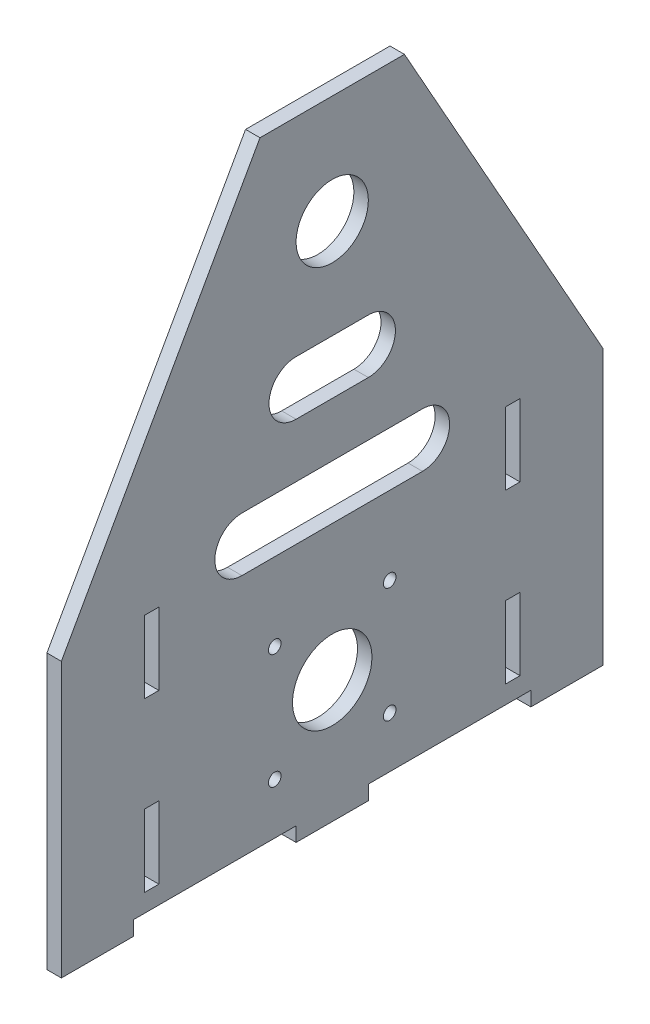
SolidWorks part; units mm, degrees
ref_plane "Front Plane" through (0, 0, 0) normal (0, 0, 1) x (1, 0, 0)
ref_plane "Top Plane" through (0, 0, 0) normal (0, 1, 0) x (1, 0, 0)
ref_plane "Right Plane" through (0, 0, 0) normal (1, 0, 0) x (0, 0, -1)
sketch "Sketch1" plane through (0, 0, 0) normal (1, 0, 0) x (0, 0, -1)
  line L0 (0, 0) -> (0, 111.6623) construction
  line L1 (-20, 170.0871) -> (20, 170.0871)
  line L2 (-55, 0.0871) -> (-10, 0.0871)
  line L3 (-75, -3.9129) -> (-75, 72.0364)
  line L4 (-75, 72.0364) -> (-20, 170.0871)
  line L5 (20, 170.0871) -> (75, 72.0364)
  line L6 (75, 72.0364) -> (75, -3.9129)
  line L7 (-75, -3.9129) -> (-55, -3.9129)
  line L8 (-55, 0.0871) -> (-55, -3.9129)
  line L9 (-10, 0.0871) -> (-10, -3.9129)
  line L10 (10, 0.0871) -> (10, -3.9129)
  line L11 (55, 0.0871) -> (55, -3.9129)
  line L12 (-10, -3.9129) -> (10, -3.9129)
  line L13 (55, -3.9129) -> (75, -3.9129)
  line L14 (10, 0.0871) -> (55, 0.0871)
  line L15 (0, 30.0871) -> (-15.9099, 45.997) construction
  line L16 (-25, 75.0871) -> (25, 75.0871) construction
  line L17 (-10, 105.0871) -> (10, 105.0871) construction
  line L18 (-10, 105.0871) -> (10, 105.0871) construction
  line L19 (-10, 112.5871) -> (10, 112.5871)
  line L20 (-10, 97.5871) -> (10, 97.5871)
  line L21 (-25, 75.0871) -> (25, 75.0871) construction
  line L22 (-25, 82.5871) -> (25, 82.5871)
  line L23 (-25, 67.5871) -> (25, 67.5871)
  line L24 (-50, 169.5343) -> (-50, -42.818) construction
  line L25 (50, 169.5343) -> (50, -42.818) construction
  line L26 (-62.1844, 15.0871) -> (92.4546, 15.0871) construction
  line L27 (-91.6692, 61.5499) -> (106.6605, 61.5499) construction
  line L28 (-52, 25.0871) -> (-48, 25.0871)
  line L29 (-52, 25.0871) -> (-52, 5.0871)
  line L30 (-52, 5.0871) -> (-48, 5.0871)
  line L31 (-48, 25.0871) -> (-48, 5.0871)
  line L32 (-52, 25.0871) -> (-48, 5.0871) construction
  line L33 (-52, 5.0871) -> (-48, 25.0871) construction
  line L34 (48, 25.0871) -> (52, 25.0871)
  line L35 (48, 25.0871) -> (48, 5.0871)
  line L36 (48, 5.0871) -> (52, 5.0871)
  line L37 (52, 25.0871) -> (52, 5.0871)
  line L38 (48, 25.0871) -> (52, 5.0871) construction
  line L39 (48, 5.0871) -> (52, 25.0871) construction
  line L41 (-52, 71.5499) -> (-48, 71.5499)
  line L42 (-52, 71.5499) -> (-52, 51.5499)
  line L43 (-52, 51.5499) -> (-48, 51.5499)
  line L44 (-48, 71.5499) -> (-48, 51.5499)
  line L45 (-52, 71.5499) -> (-48, 51.5499) construction
  line L46 (-52, 51.5499) -> (-48, 71.5499) construction
  line L47 (52, 51.5499) -> (48, 51.5499)
  line L48 (52, 51.5499) -> (52, 71.5499)
  line L49 (52, 71.5499) -> (48, 71.5499)
  line L50 (48, 51.5499) -> (48, 71.5499)
  line L51 (52, 51.5499) -> (48, 71.5499) construction
  line L52 (52, 71.5499) -> (48, 51.5499) construction
  circle A0 centre (0, 30.0871) radius 11
  circle A1 centre (0, 140.0871) radius 10
  circle A2 centre (0, 30.0871) radius 22.5 construction
  circle A3 centre (-15.9099, 45.997) radius 1.75
  circle A4 centre (-15.9099, 14.1772) radius 1.75
  circle A5 centre (15.9099, 14.1772) radius 1.75
  circle A6 centre (15.9099, 45.997) radius 1.75
  arc A7 (-10, 112.5871) -> (-10, 97.5871) centre (-10, 105.0871) ccw
  arc A8 (10, 97.5871) -> (10, 112.5871) centre (10, 105.0871) ccw
  arc A9 (-25, 82.5871) -> (-25, 67.5871) centre (-25, 75.0871) ccw
  arc A10 (25, 67.5871) -> (25, 82.5871) centre (25, 75.0871) ccw
  circle A11 centre (0, 140.0871) radius 80 construction
  point P33 (0, 30.0871)
  point P35 (0, 105.0871)
  point P40 (0, 75.0871)
  point P52 (-50, 15.0871)
  point P57 (50, 15.0871)
  point P64 (-50, 61.5499)
  point P69 (50, 61.5499)
  dimension "D8" = 22
  dimension "D11" = 20
  dimension "D12" = 45
  dimension "D13" = 3.5
  dimension "D23" = 160
  dimension "D1" = 170
  dimension "D2" = 150
  dimension "D3" = 40
  dimension "D4" = 4
  dimension "D5" = 20
  dimension "D6" = 20
  dimension "D7" = 20
  dimension "D9" = 30
  dimension "D10" = 140
  dimension "D15" = 50
  dimension "D16" = 20
  dimension "D17" = 45
  dimension "D18" = 30
  dimension "D19" = 15
  dimension "D20" = 15
  dimension "D21" = 100
  dimension "D22" = 50
  dimension "D24" = 15
  dimension "D25" = 4
  dimension "D26" = 20
  dimension "D27" = 20
  dimension "D28" = 4
  dimension "D29" = 20
  dimension "D30" = 20
  dimension "D14" = 4
extrude "Boss-Extrude1" add sketch "Sketch1" along normal blind 4
